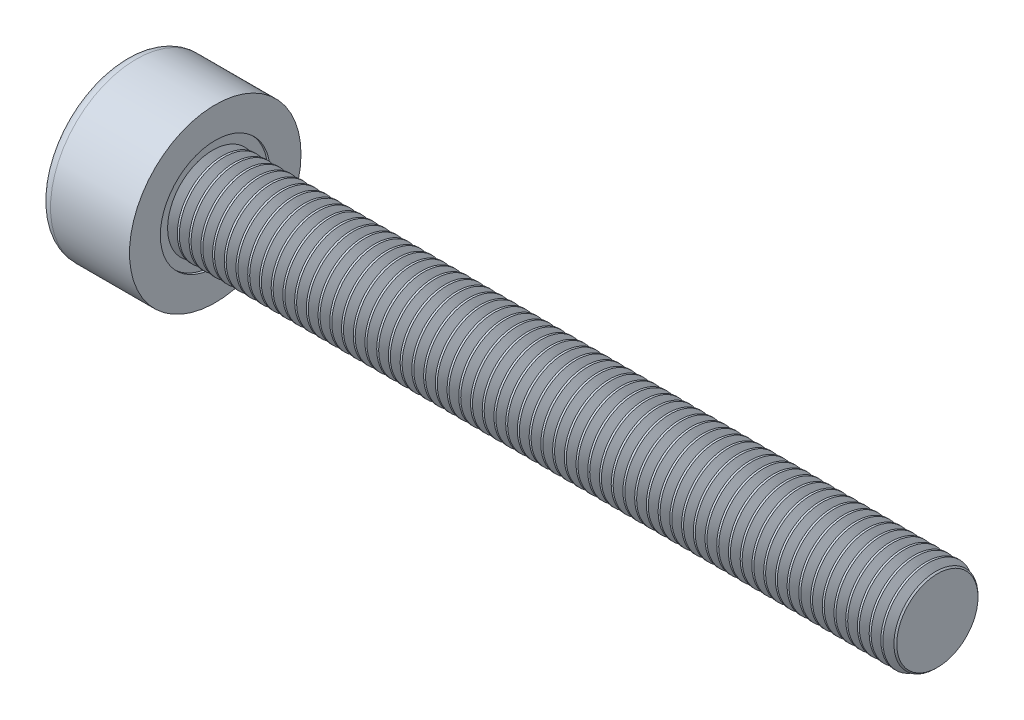
SolidWorks part; units mm, degrees
ref_plane "Front" through (0, 0, 0) normal (0, 0, 1) x (1, 0, 0)
ref_plane "Top" through (0, 0, 0) normal (0, 1, 0) x (1, 0, 0)
ref_plane "Right" through (0, 0, 0) normal (1, 0, 0) x (0, 0, -1)
sketch "Sketch1" plane through (0, 0, 0) normal (1, 0, 0) x (0, 0, -1)
  circle A0 centre (0, 0) radius 1.9
  dimension "dk" = 3.8
extrude "BaseHead" add sketch "Sketch1" along normal blind 2
sketch "Sketch2" plane through (2, 0, 0) normal (1, 0, 0) x (0, 0, -1)
  circle A0 centre (0, 0) radius 1
  dimension "d" = 2
extrude "BaseBody" add sketch "Sketch2" along normal blind 16
cosmetic thread "ThreadCosmetic1" [suppressed] parameters "b"=16, "D2"=1.567
sketch "Sketch3" plane through (0, 0, 0) normal (1, 0, 0) x (0, 0, -1)
  line L1 (0.866, 0) -> (0.433, 0.75)
  line L2 (0.433, 0.75) -> (-0.433, 0.75)
  line L3 (-0.433, 0.75) -> (-0.866, 0)
  line L4 (-0.866, 0) -> (-0.433, -0.75)
  line L5 (-0.433, -0.75) -> (0.433, -0.75)
  line L6 (0.433, -0.75) -> (0.866, 0)
  circle A0 centre (0, 0) radius 0.75 construction
  dimension "s" = 1.5
  dimension "e" = 1.7321
extrude "HexagonSocket" cut sketch "Sketch3" along normal blind 1
sketch "Sketch4" plane through (-4.1961, 0.75, 0) normal (0, 0, 1) x (-1, 0, 0)
  line L0 (-5.1961, 1.5) -> (-5.6292, 0.75)
  line L2 (-5.6292, 0.75) -> (-5.1961, 0.75)
  line L3 (-5.1961, 0.75) -> (-5.1961, 1.5)
  line L4 (-5.0351, 0.75) -> (0.839, 0.75) construction
  line L5 (-22.1961, 0.75) -> (-6.1961, 0.75) construction
  line L6 (-6.1961, 0.75) -> (-4.1961, 0.75) construction
  dimension "m" = 60
revolve "Cut-Revolve1" cut sketch "Sketch4" angle 360 about L4
fillet "HeadFillet" [suppressed] radius 0.1
fillet "TopFillet" radius 0.25 1 edges at (0, 0, -1.9)
chamfer "Chamfer1" distance 0.1 angle 45 1 edges at (18, 0, -1)
sketch "Sketch5" plane through (0, 0, 0) normal (0, 0, 1) x (1, 0, 0)
  line L0 (17.9, 0.8125) -> (18.0083, 1)
  line L1 (18.0083, 1) -> (18.0083, 1.2165)
  line L2 (18.0083, 1.2165) -> (17.7918, 1.2165)
  line L3 (17.7918, 1.2165) -> (17.7918, 1)
  line L4 (17.7918, 1) -> (17.9, 0.8125)
  line L5 (0, 0) -> (7.8886, 0) construction
  line L6 (17.9, -1) -> (17.9, 1) construction
  dimension "D1" = 2
  dimension "D2" = 0.2165
revolve "Cut-Revolve10" cut sketch "Sketch5" angle 360 about L5
pattern_linear "LPattern10" count 62 spacing 0.2598 along (-1, 0, 0) of "Cut-Revolve10"
equation "\"r1@TopFillet\" = \"d@Sketch2\" / 8"
equation "\"D1@Chamfer1\" = \"r@HeadFillet\""
equation "\"D1@Sketch5\" = \"d@Sketch2\""
equation "\"D2@Sketch5\" =  ( \"d@Sketch2\" - \"D2@ThreadCosmetic1\" )  / 2"
equation "\"D3@LPattern10\" = \"D2@Sketch5\" * 1.2"
equation "\"D1@LPattern10\" = \"b@ThreadCosmetic1\" / \"D3@LPattern10\""
